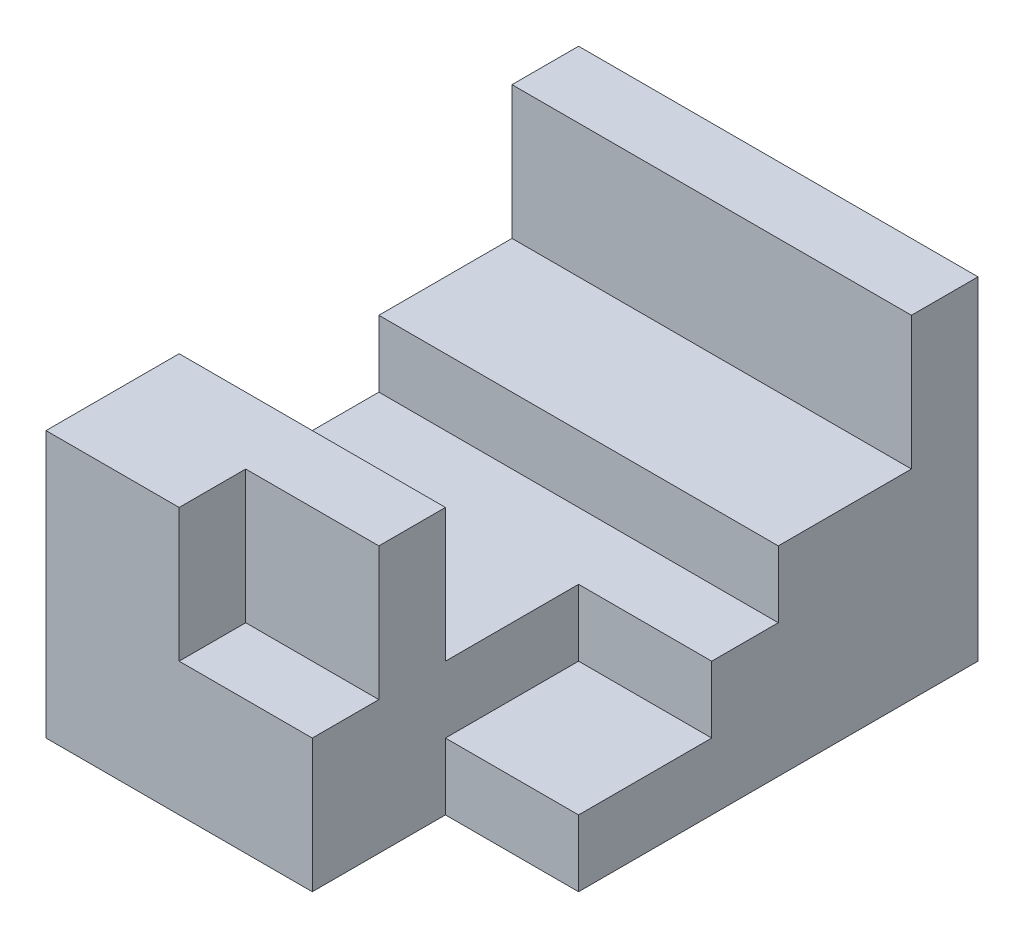
SolidWorks part; units mm, degrees
ref_plane "Front Plane" through (0, 0, 0) normal (0, 0, 1) x (1, 0, 0)
ref_plane "Top Plane" through (0, 0, 0) normal (0, 1, 0) x (1, 0, 0)
ref_plane "Right Plane" through (0, 0, 0) normal (1, 0, 0) x (0, 0, -1)
sketch "Sketch1" plane through (0, 0, 0) normal (0, 0, 1) x (1, 0, 0)
  line L1 (3, -2.5) -> (-3, -2.5)
  line L2 (3, -2.5) -> (3, 2.5)
  line L3 (3, 2.5) -> (-3, 2.5)
  line L4 (-3, -2.5) -> (-3, 2.5)
  line L5 (3, -2.5) -> (-3, 2.5) construction
  line L6 (3, 2.5) -> (-3, -2.5) construction
  point P0 (0, 0)
  dimension "D1" = 6
  dimension "D2" = 5
extrude "Boss-Extrude1" add sketch "Sketch1" along normal blind 8
sketch "Sketch3" plane through (0, 0, 8) normal (0, 0, 1) x (1, 0, 0)
  line L0 (3, -2.5) -> (1, -2.5)
  line L1 (-3, -2.5) -> (3, -2.5) construction
  line L2 (1, -2.5) -> (1, 2.5)
  line L3 (3, 2.5) -> (-3, 2.5) construction
  line L4 (1, 2.5) -> (3, 2.5)
  line L5 (3, 2.5) -> (3, -2.5)
  dimension "D1" = 2
extrude "Cut-Extrude1" cut sketch "Sketch3" against normal blind 2
sketch "Sketch4" plane through (0, 0, 8) normal (0, 0, 1) x (1, 0, 0)
  line L0 (1, 2.5) -> (-1, 2.5)
  line L1 (1, 2.5) -> (-3, 2.5) construction
  line L2 (-1, 2.5) -> (-1, 0.5)
  line L3 (-1, 0.5) -> (1, 0.5)
  line L4 (1, 2.5) -> (1, 0.5)
  line L5 (1, 2.5) -> (1, -2.5) construction
  dimension "D1" = 2
  dimension "D2" = 2
extrude "Cut-Extrude2" cut sketch "Sketch4" against normal blind 1
sketch "Sketch5" plane through (0, 2.5, 0) normal (0, 1, 0) x (1, 0, 0)
  line L0 (3, -1) -> (-3, -1)
  line L1 (3, -6) -> (3, 0) construction
  line L2 (-3, -8) -> (-3, 0) construction
  line L3 (-3, -1) -> (-3, -6)
  line L4 (-3, -6) -> (3, -6)
  line L5 (3, -6) -> (3, -1)
  dimension "D1" = 1
extrude "Cut-Extrude3" cut sketch "Sketch5" against normal blind 2
sketch "Sketch6" plane through (0, 0.5, 0) normal (0, 1, 0) x (1, 0, 0)
  line L0 (3, -6) -> (3, -4)
  line L1 (3, -6) -> (3, -1) construction
  line L2 (3, -4) -> (1, -4)
  line L3 (1, -4) -> (1, -6)
  line L4 (-3, -6) -> (1, -6) construction
  line L5 (1, -6) -> (3, -6)
  dimension "D1" = 2
  dimension "D2" = 2
extrude "Cut-Extrude4" cut sketch "Sketch6" against normal blind 2
sketch "Sketch7" plane through (0, 0.5, 0) normal (0, 1, 0) x (1, 0, 0)
  line L0 (3, -4) -> (3, -3)
  line L1 (3, -4) -> (3, -1) construction
  line L2 (3, -3) -> (-3, -3)
  line L3 (-3, -3) -> (-3, -6)
  line L4 (-3, -6) -> (1, -6)
  line L5 (1, -6) -> (1, -4)
  line L6 (1, -4) -> (3, -4)
  line L7 (-3, -1) -> (-3, -6) construction
  dimension "D1" = 1
  dimension "D2" = 3
extrude "Cut-Extrude5" cut sketch "Sketch7" against normal blind 1
sketch "Sketch8" plane through (0, 2.5, 0) normal (0, 1, 0) x (1, 0, 0)
  line L1 (-5.1535, -5.705) -> (3.3819, -5.705)
  line L2 (-5.1535, -5.705) -> (-5.1535, -9.1921)
  line L3 (-5.1535, -9.1921) -> (3.3819, -9.1921)
  line L4 (3.3819, -5.705) -> (3.3819, -9.1921)
extrude "Cut-Extrude6" cut sketch "Sketch8" against normal blind 1
sketch "Sketch9" plane through (0, 0.5, 0) normal (0, 1, 0) x (1, 0, 0)
  line L1 (-1, -7) -> (1, -7)
  line L2 (-1, -7) -> (-1, -8)
  line L3 (-1, -8) -> (1, -8)
  line L4 (1, -7) -> (1, -8)
extrude "Cut-Extrude7" cut sketch "Sketch9" against normal blind 1
